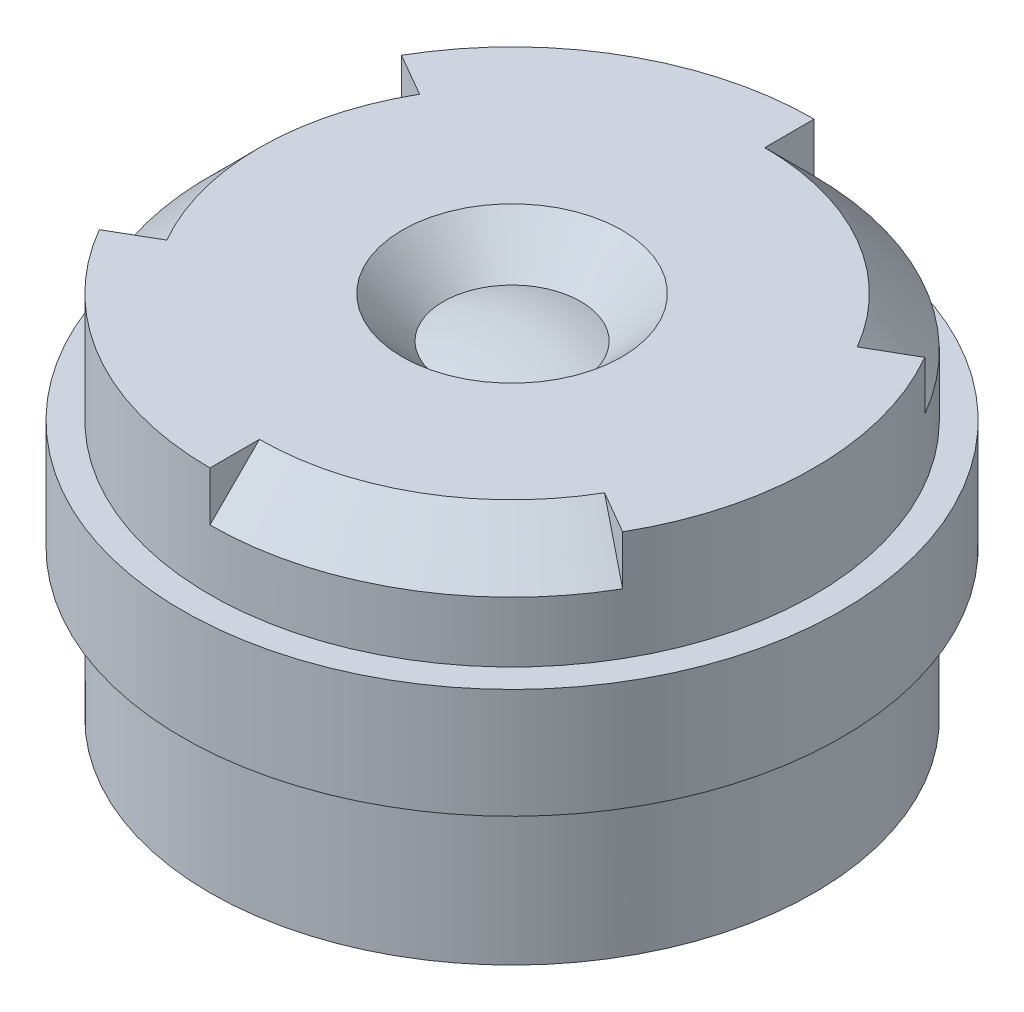
SolidWorks part; units mm, degrees
material "ABS PC"
ref_plane "Vorne" through (0, 0, 0) normal (0, 0, 1) x (1, 0, 0)
ref_plane "Oben" through (0, 0, 0) normal (0, 1, 0) x (1, 0, 0)
ref_plane "Rechts" through (0, 0, 0) normal (1, 0, 0) x (0, 0, -1)
sketch "Skizze3" plane through (0, 0, 0) normal (0, 0, 1) x (1, 0, 0)
  line L0 (0, 0) -> (0, -2.1568) construction
  line L1 (1, 0.8) -> (2.75, 0.8)
  line L2 (2.75, 0.8) -> (2.75, -2.55)
  line L3 (2.75, -2.55) -> (2.1, -2.55)
  line L4 (1, 0.8) -> (0.625, 0.425)
  line L5 (0.8125, 0.6125) -> (0.8125, 0.8) construction
  line L6 (0.8125, 0.8) -> (1, 0.8) construction
  line L7 (2.1, -2.55) -> (1.8, -2.25)
  line L8 (2.1, -2.55) -> (2.1, -2.4) construction
  line L9 (2.1, -2.4) -> (1.95, -2.4) construction
  line L10 (0, -2.55) -> (0, 0.525)
  arc A0 (1.8, -2.25) -> (0, -2.55) centre (0, 3) cw
  arc A1 (0, 0.525) -> (0.625, 0.425) centre (0, -1.4781) cw
  dimension "D6" = 0.1
  dimension "D1" = 3.35
  dimension "D2" = 5.5
  dimension "D3" = 2
  dimension "D4" = 1.25
  dimension "D5" = 3.6
  dimension "D7" = 0.8
  dimension "D8" = 0.3
revolve "Body" add sketch "Skizze3" angle 360 about L0
sketch "Skizze4" plane through (0, 0, 0) normal (0, 0, 1) x (1, 0, 0)
  line L0 (0, 0) -> (0, 1.3093) construction
  line L1 (2.75, -2.55) -> (2.75, 0.8) construction
  line L2 (2.75, -0.2) -> (3, -0.2)
  line L3 (2.75, -0.2) -> (2.75, -1.2)
  line L4 (2.75, -1.2) -> (3, -1.2)
  line L5 (3, -0.2) -> (3, -1.2)
  line L6 (2.75, 0.8) -> (-2.75, 0.8) construction
  dimension "D1" = 2
  dimension "D2" = 1
  dimension "D3" = 6
revolve "Thread" add sketch "Skizze4" angle 360 about L0
sketch "Skizze5" plane through (0, 0, 0) normal (1, 0, 0) x (0, 0, -1)
  line L0 (0, 0) -> (0, -3.7681) construction
  line L1 (2.75, 0.8) -> (2.75, 0.35)
  line L2 (2.75, -0.2) -> (2.75, 0.8) construction
  line L3 (2.75, 0.35) -> (2.3, 0.8)
  line L4 (2.75, 0.8) -> (-2.75, 0.8) construction
  line L5 (2.3, 0.8) -> (2.75, 0.8)
  dimension "D1" = 0.45
revolve "Toolface" cut sketch "Skizze5" angle 60 about L0
pattern_circular "Kreismuster1" count 3 over 360 about axis through (0, 0, 0) along (0, 1, 0) of "Toolface"
